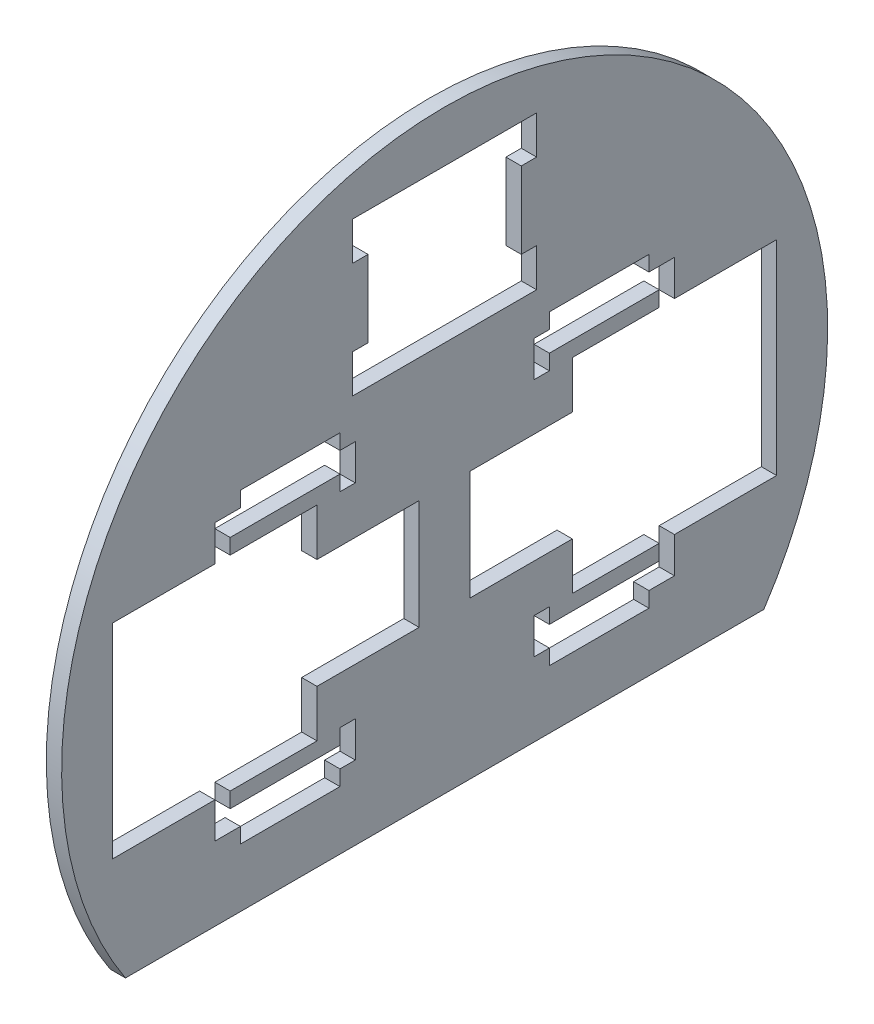
SolidWorks part; units mm, degrees
ref_plane "Front Plane" through (0, 0, 0) normal (0, 0, 1) x (1, 0, 0)
ref_plane "Top Plane" through (0, 0, 0) normal (0, 1, 0) x (1, 0, 0)
ref_plane "Right Plane" through (0, 0, 0) normal (1, 0, 0) x (0, 0, -1)
sketch "Sketch1" plane through (0, 0, 0) normal (1, 0, 0) x (0, 0, -1)
  line L0 (-125, -82.9156) -> (125, -82.9156)
  arc A0 (125, -82.9156) -> (-125, -82.9156) centre (0, 0) ccw
  dimension "D1" = 300
  dimension "D2" = 250
extrude "Boss-Extrude1" add sketch "Sketch1" along normal blind 6
sketch "Sketch2" plane through (6, 0, 0) normal (1, 0, 0) x (0, 0, -1)
  line L0 (0, 0) -> (0, -74.2453) construction
  line L1 (-130, 40) -> (-50, 40)
  line L2 (-130, 40) -> (-130, -40)
  line L3 (-130, -40) -> (-50, -40)
  line L4 (-50, 40) -> (-50, -40)
  line L5 (-130, 40) -> (-50, -40) construction
  line L6 (-130, -40) -> (-50, 40) construction
  line L7 (130, -40) -> (50, -40)
  line L8 (50, 40) -> (50, -40)
  line L9 (130, 40) -> (50, 40)
  line L10 (130, 40) -> (130, -40)
  arc A0 (125, -82.9156) -> (-125, -82.9156) centre (0, 0) ccw construction
  point P0 (-90, 0)
  dimension "D1" = 80
  dimension "D2" = 80
  dimension "D3" = 90
extrude "Cut-Extrude1" cut sketch "Sketch2" against normal blind 6
sketch "Sketch3" plane through (6, 0, 0) normal (1, 0, 0) x (0, 0, -1)
  line L1 (-30, 130) -> (30, 130)
  line L2 (-30, 130) -> (-30, 70)
  line L3 (-30, 70) -> (30, 70)
  line L4 (30, 130) -> (30, 70)
  line L5 (-30, 130) -> (30, 70) construction
  line L6 (-30, 70) -> (30, 130) construction
  point P0 (0, 100)
  dimension "D1" = 60
  dimension "D2" = 70
extrude "Cut-Extrude2" cut sketch "Sketch3" against normal blind 6
sketch "Sketch4" plane through (6, 0, 0) normal (1, 0, 0) x (0, 0, -1)
  line L0 (-130, -40) -> (-50, -40) construction
  line L1 (-90, -40) -> (-84, -40)
  line L2 (-90, -40) -> (-90, -54)
  line L3 (-80, -60) -> (-41, -60)
  line L4 (-35, -40) -> (-35, -54)
  line L5 (-35, -54) -> (-41, -54)
  line L7 (-130, 0) -> (0, 0) construction
  line L8 (-130, 40) -> (-130, -40) construction
  line L9 (-80, 60) -> (-41, 60)
  line L10 (-35, 40) -> (-35, 54)
  line L11 (-90, 40) -> (-84, 40)
  line L12 (-90, 40) -> (-90, 54)
  line L13 (0, 0) -> (0, 30.7351) construction
  line L14 (80, -60) -> (41, -60)
  line L15 (35, -40) -> (35, -54)
  line L16 (90, -40) -> (84, -40)
  line L17 (90, -40) -> (90, -54)
  line L18 (90, 40) -> (90, 54)
  line L19 (90, 40) -> (84, 40)
  line L20 (35, 40) -> (35, 54)
  line L21 (80, 60) -> (41, 60)
  line L22 (-50, -40) -> (-50, 40) construction
  line L26 (-90, 54) -> (-80, 54)
  line L27 (-80, 60) -> (-80, 54)
  line L28 (-35, 54) -> (-41, 54)
  line L29 (-41, 60) -> (-41, 54)
  line L30 (-41, -60) -> (-41, -54)
  line L33 (-90, -54) -> (-80, -54)
  line L34 (-80, -60) -> (-80, -54)
  line L38 (41, -60) -> (41, -54)
  line L39 (35, -54) -> (41, -54)
  line L42 (80, -60) -> (80, -54)
  line L43 (90, -54) -> (80, -54)
  line L45 (35, 54) -> (41, 54)
  line L46 (41, 60) -> (41, 54)
  line L49 (90, 54) -> (80, 54)
  line L50 (80, 60) -> (80, 54)
  line L53 (-41, -40) -> (-41, -46)
  line L54 (-41, -46) -> (-84, -46)
  line L55 (-84, -40) -> (-84, -46)
  line L56 (-41, 46) -> (-84, 46)
  line L57 (-84, 40) -> (-84, 46)
  line L59 (-41, 40) -> (-41, 46)
  line L60 (41, -46) -> (84, -46)
  line L61 (84, -40) -> (84, -46)
  line L63 (41, -40) -> (41, -46)
  line L64 (41, 40) -> (41, 46)
  line L66 (84, 40) -> (84, 46)
  line L67 (41, 46) -> (84, 46)
  line L68 (-41, 40) -> (-35, 40)
  line L69 (-41, -40) -> (-35, -40)
  line L70 (41, 40) -> (35, 40)
  line L71 (41, -40) -> (35, -40)
  point P4 (-90, -47)
  point P7 (-90, -40)
  dimension "D1" = 20
  dimension "D2" = 6
  dimension "D3" = 15
  dimension "D4" = 6
  dimension "D5" = 10
  dimension "D6" = 6
  dimension "D7" = 6
  dimension "D8" = 6
extrude "Cut-Extrude3" cut sketch "Sketch4" against normal blind 10
sketch "Sketch6" plane through (6, 0, 0) normal (1, 0, 0) x (0, 0, -1)
  line L0 (-50, -40) -> (-50, 40) construction
  line L1 (-50, 21.5) -> (-10, 21.5)
  line L2 (-50, 21.5) -> (-50, -21.5)
  line L3 (-50, -21.5) -> (-10, -21.5)
  line L4 (-10, 21.5) -> (-10, -21.5)
  line L5 (50, 40) -> (50, -40) construction
  line L6 (50, 21.5) -> (10, 21.5)
  line L7 (50, 21.5) -> (50, -21.5)
  line L8 (50, -21.5) -> (10, -21.5)
  line L9 (10, 21.5) -> (10, -21.5)
  point P13 (-10, 0)
  dimension "D1" = 40
  dimension "D2" = 43
extrude "Cut-Extrude4" cut sketch "Sketch6" against normal through all
sketch "Sketch7" plane through (6, 0, 0) normal (1, 0, 0) x (0, 0, -1)
  line L0 (0, 130) -> (0, 67.4694) construction
  line L1 (-30, 130) -> (-36, 130)
  line L2 (-30, 130) -> (-30, 115)
  line L3 (-30, 115) -> (-36, 115)
  line L4 (-36, 130) -> (-36, 115)
  line L5 (-30, 70) -> (-36, 70)
  line L6 (-30, 70) -> (-30, 85)
  line L7 (-30, 85) -> (-36, 85)
  line L8 (-36, 70) -> (-36, 85)
  line L9 (30, 130) -> (-30, 130) construction
  line L10 (30, 85) -> (36, 85)
  line L11 (36, 70) -> (36, 85)
  line L12 (30, 70) -> (36, 70)
  line L13 (30, 70) -> (30, 85)
  line L14 (30, 115) -> (36, 115)
  line L15 (36, 130) -> (36, 115)
  line L16 (30, 130) -> (36, 130)
  line L17 (30, 130) -> (30, 115)
  dimension "D1" = 6
  dimension "D2" = 15
extrude "Cut-Extrude5" cut sketch "Sketch7" against normal through all
